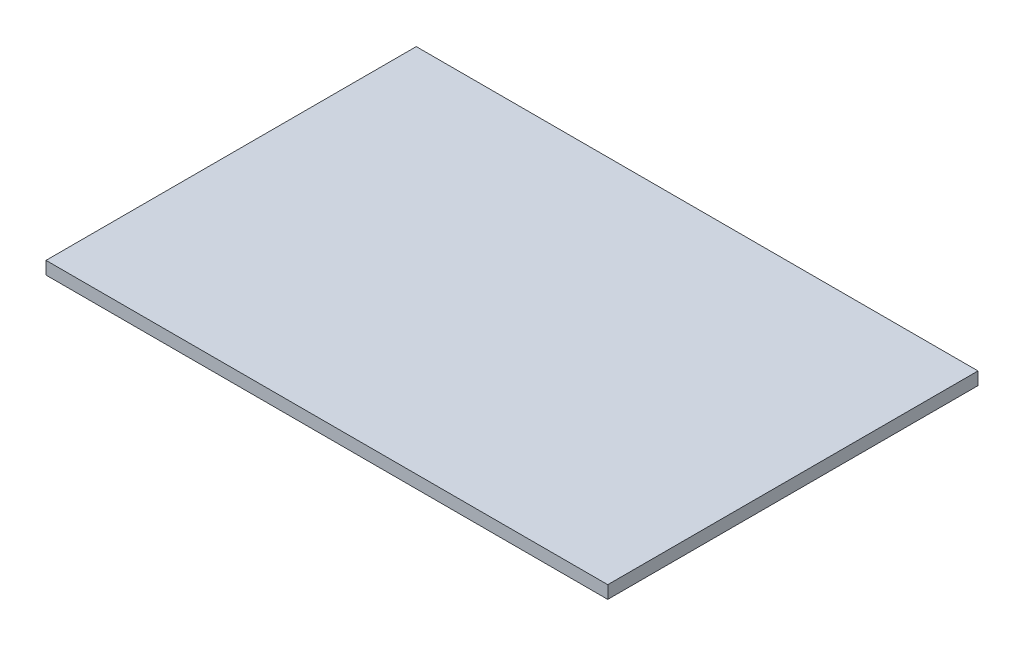
SolidWorks part; units mm, degrees
ref_plane "Front Plane" through (0, 0, 0) normal (0, 0, 1) x (1, 0, 0)
ref_plane "Top Plane" through (0, 0, 0) normal (0, 1, 0) x (1, 0, 0)
ref_plane "Right Plane" through (0, 0, 0) normal (1, 0, 0) x (0, 0, -1)
sketch "Sketch1" plane through (0, 0, 0) normal (0, 1, 0) x (1, 0, 0)
  line L1 (0, 0) -> (220, 0)
  line L2 (0, 0) -> (0, 145)
  line L3 (0, 145) -> (220, 145)
  line L4 (220, 0) -> (220, 145)
  dimension "D1" = 220
  dimension "D2" = 145
extrude "Boss-Extrude1" add sketch "Sketch1" along normal blind 5
